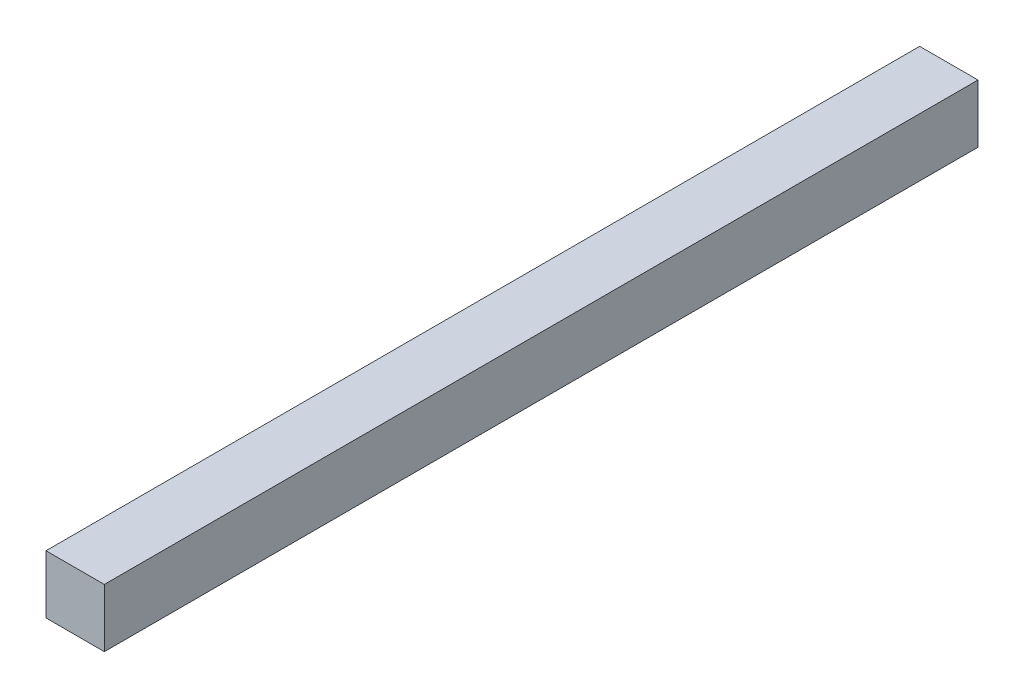
SolidWorks part; units mm, degrees
ref_plane "Plano frontal" through (0, 0, 0) normal (0, 0, 1) x (1, 0, 0)
ref_plane "Plano superior" through (0, 0, 0) normal (0, 1, 0) x (1, 0, 0)
ref_plane "Plano direito" through (0, 0, 0) normal (1, 0, 0) x (0, 0, -1)
sketch "Esboço2" plane through (0, 0, 0) normal (0, 0, 1) x (1, 0, 0)
  line L1 (-110.6583, 30) -> (-80.6129, 30)
  line L2 (-110.6583, 30) -> (-110.6583, 0)
  line L3 (-110.6583, 0) -> (-80.6129, 0)
  line L4 (-80.6129, 30) -> (-80.6129, 0)
  dimension "D1" = 30
  dimension "D2" = 30.0454
extrude "Ressalto-extrusão1" add sketch "Esboço2" along normal mid plane 450
